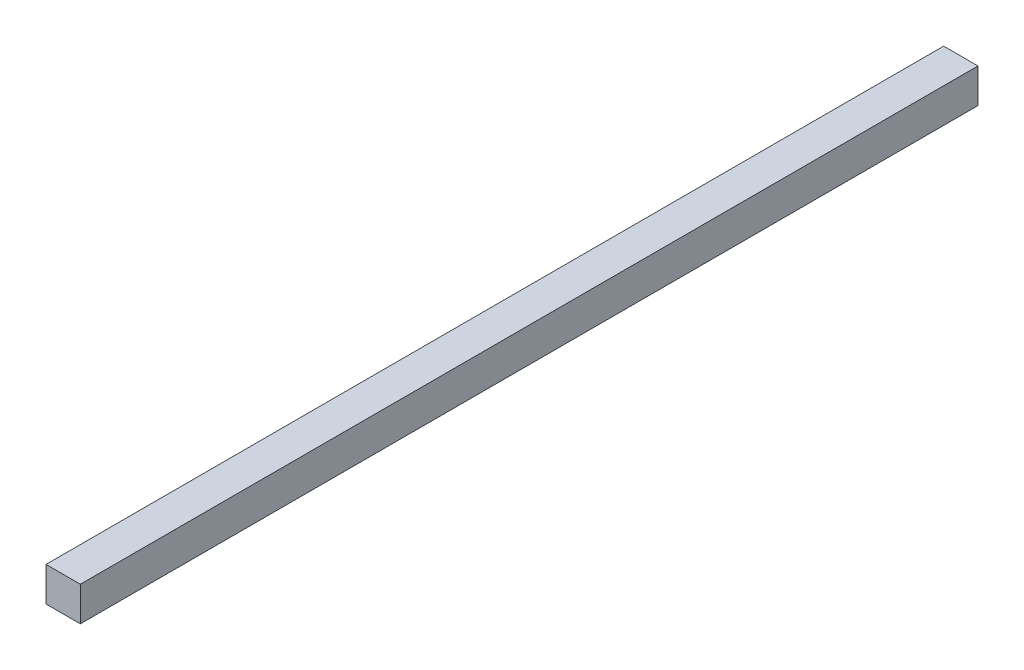
SolidWorks part; units mm, degrees
ref_plane "Front Plane" through (0, 0, 0) normal (0, 0, 1) x (1, 0, 0)
ref_plane "Top Plane" through (0, 0, 0) normal (0, 1, 0) x (1, 0, 0)
ref_plane "Right Plane" through (0, 0, 0) normal (1, 0, 0) x (0, 0, -1)
sketch "Sketch1" plane through (0, 0, 0) normal (0, 0, 1) x (1, 0, 0)
  line L1 (-10, -10) -> (10, -10)
  line L2 (-10, -10) -> (-10, 10)
  line L3 (-10, 10) -> (10, 10)
  line L4 (10, -10) -> (10, 10)
  line L5 (-10, -10) -> (10, 10) construction
  line L6 (-10, 10) -> (10, -10) construction
  point P0 (0, 0)
  dimension "D1" = 20
extrude "Boss-Extrude1" add sketch "Sketch1" along normal blind 523
